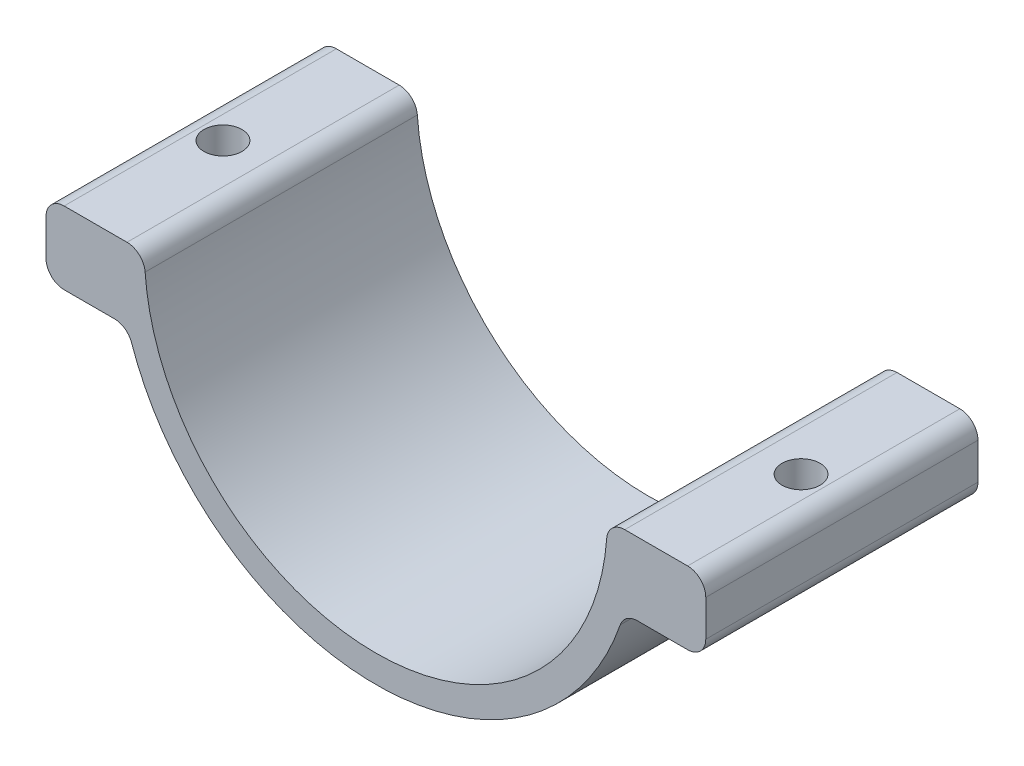
SolidWorks part; units mm, degrees
ref_plane "Front Plane" through (0, 0, 0) normal (0, 0, 1) x (1, 0, 0)
ref_plane "Top Plane" through (0, 0, 0) normal (0, 1, 0) x (1, 0, 0)
ref_plane "Right Plane" through (0, 0, 0) normal (1, 0, 0) x (0, 0, -1)
sketch "Sketch2" plane through (0, 0, 0) normal (0, 0, 1) x (1, 0, 0)
  circle A0 centre (0, 0) radius 25.2 construction
  dimension "D1" = 50.4
sketch "Sketch3" plane through (0, 0, 0) normal (0, 0, 1) x (1, 0, 0)
  line L0 (-25.5, 0) -> (-36.3542, 0)
  line L1 (25.5, 0) -> (36.3542, 0)
  line L11 (27.3542, -8) -> (36.3542, -8)
  line L12 (36.3542, -8) -> (36.3542, 0)
  line L13 (-27.3542, -8) -> (-36.3542, -8)
  line L14 (-36.3542, -8) -> (-36.3542, 0)
  line L15 (31.8542, -8) -> (31.8542, 0) construction
  line L16 (28.8542, -4) -> (34.8542, -4) construction
  arc A2 (25.5, 0) -> (-25.5, 0) centre (0, 0) cw
  circle A3 centre (0, 0) radius 25.2 construction
  arc A8 (-27.3542, -8) -> (27.3542, -8) centre (0, 0) ccw
  point P24 (31.8542, -4)
  dimension "D1" = 0.3
  dimension "D7" = 3
  dimension "D8" = 8
  dimension "D9" = 6
  dimension "D10" = 1.5
  dimension "D11" = 1.5
  dimension "D12" = 0
extrude "Boss-Extrude1" add sketch "Sketch3" along normal blind 30
sketch "Sketch5" plane through (0, 0, 0) normal (0, -1, 0) x (1, 0, 0)
  line L0 (28.8542, 0) -> (34.8542, 0) construction
  line L1 (28.8542, 0) -> (34.8542, 0) construction
  line L2 (31.8542, 0) -> (31.8542, 30) construction
  line L3 (36.3542, 30) -> (25.5, 30) construction
  line L4 (0, 0) -> (0, 30) construction
  line L5 (25.2, 0) -> (-25.2, 0) construction
  line L6 (25.5, 30) -> (-25.5, 30) construction
  circle A0 centre (31.8542, 15) radius 2.1
  dimension "D1" = 4.2
extrude "Cut-Extrude1" cut sketch "Sketch5" along normal blind 5
sketch "Sketch6" plane through (0, 0, 0) normal (0, 1, 0) x (1, 0, 0)
  circle A0 centre (31.8542, -15) radius 1.65
  dimension "D1" = 3.3
extrude "Cut-Extrude2" cut sketch "Sketch6" against normal through all
mirror "Mirror1" about plane through (0, 0, 0) normal (1, 0, 0) of "Cut-Extrude2", "Cut-Extrude1"
fillet "Fillet1" radius 2 8 edges at (-25.5, 0, 15) (25.5, 0, 15) (27.3542, -8, 15) (-27.3542, -8, 15) (-36.3542, -8, 15) (-36.3542, 0, 15) (36.3542, -8, 15) (36.3542, 0, 15)
